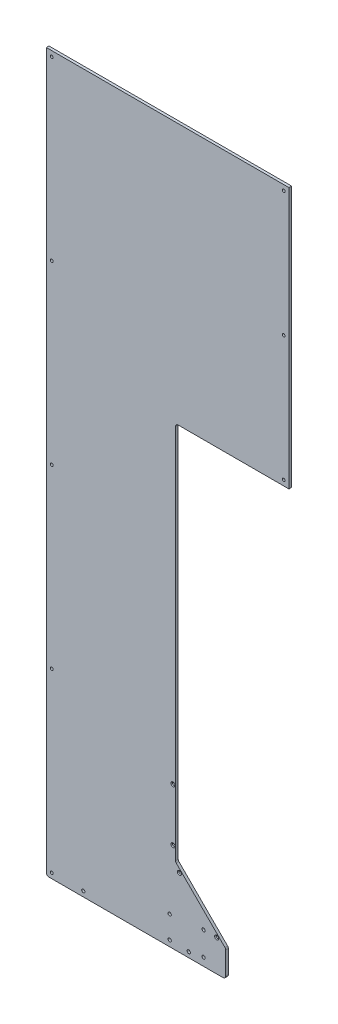
SolidWorks part; units mm, degrees
material "PC High Viscosity"
ref_plane "Front Plane" through (0, 0, 0) normal (0, 0, 1) x (1, 0, 0)
ref_plane "Top Plane" through (0, 0, 0) normal (0, 1, 0) x (1, 0, 0)
ref_plane "Right Plane" through (0, 0, 0) normal (1, 0, 0) x (0, 0, -1)
sketch "Sketch2" plane through (0, 0, 0) normal (0, 0, 1) x (1, 0, 0)
  line L1 (0, 0) -> (584.2, 0)
  line L2 (0, 0) -> (0, 1727.2)
  line L3 (0, 1727.2) -> (584.2, 1727.2)
  line L4 (584.2, 0) -> (584.2, 1727.2)
  dimension "D1" = 584.2
  dimension "D2" = 1727.2
extrude "Boss-Extrude1" add sketch "Sketch2" along normal blind 6.35
sketch "Sketch3" plane through (0, 0, 6.35) normal (0, 0, 1) x (1, 0, 0)
  line L0 (584.2, 1098.55) -> (311.15, 1098.55)
  line L1 (584.2, 0) -> (584.2, 1727.2) construction
  line L2 (311.15, 1098.55) -> (311.15, 184.15)
  line L5 (431.8, 56.7648) -> (333.3633, 155.2015) construction
  line L6 (584.2, 0) -> (431.8, 0)
  line L7 (584.2, 0) -> (584.2, 1098.55)
  line L8 (584.2, 1727.2) -> (0, 1727.2) construction
  line L9 (0, 1727.2) -> (0, 0) construction
  line L10 (311.15, 184.15) -> (431.8, 63.5)
  line L11 (431.8, 63.5) -> (431.8, 0)
  circle A0 centre (584.2, 241.3) radius 241.3 construction
  dimension "D3" = 241.3
  dimension "D5" = 482.6
  dimension "D7" = 431.8
  dimension "D1" = 628.65
  dimension "D2" = 311.15
  dimension "D4" = 584.2
  dimension "D6" = 273.05
  dimension "D8" = 63.5
  dimension "D9" = 135
  dimension "D10" = 9.525
  dimension "D11" = 56.7648
  dimension "D12" = 170.6249
extrude "Cut-Extrude1" cut sketch "Sketch3" against normal through all
sketch "Sketch4" plane through (0, 0, 6.35) normal (0, 0, 1) x (1, 0, 0)
  line L0 (0, 1727.2) -> (0, 0) construction
  line L1 (584.2, 1098.55) -> (584.2, 1727.2) construction
  line L2 (584.2, 1727.2) -> (0, 1727.2) construction
  point P0 (12.7, 1714.5)
  point P1 (12.7, 1289.05)
  point P2 (12.7, 863.6)
  point P3 (12.7, 438.15)
  point P4 (12.7, 12.7)
  point P5 (571.5, 1111.25)
  point P6 (571.5, 1412.875)
  point P7 (571.5, 1714.5)
  dimension "D1" = 12.7
  dimension "D2" = 12.7
  dimension "D3" = 12.7
  dimension "D4" = 301.625
  dimension "D5" = 603.25
  dimension "D6" = 425.45
  dimension "D7" = 425.45
  dimension "D8" = 425.45
  dimension "D9" = 425.45
hole_wizard "H (0.266) Diameter Hole1" positions "Sketch5" profile "Sketch6" hole size "H" standard "ANSI Inch" end condition through all
sketch "Sketch5" plane through (0, 0, 6.35) normal (0, 0, 1) x (1, 0, 0)
  point P0 (12.7, 1714.5)
  point P3 (12.7, 1289.05)
  point P6 (12.7, 863.6)
  point P9 (12.7, 438.15)
  point P12 (12.7, 12.7)
  point P15 (571.5, 1111.25)
  point P18 (571.5, 1412.875)
  point P21 (571.5, 1714.5)
sketch "Sketch6" plane through (12.7, 1714.5, 6.35) normal (1, 0, 0) x (0, -1, 0)
  line L0 (0, 0) -> (0, 6.35)
  line L1 (0, 6.35) -> (3.3782, 6.35)
  line L2 (3.3782, 6.35) -> (3.3782, 0)
  line L5 (3.3782, 0) -> (0, 0)
  line L11 (0, -6.35) -> (0, 107.95) construction
  dimension "Thru Hole Dia." = 6.7564
  dimension "Thru Hole Depth" = 6.35
fillet "Fillet1" radius 6.35 5 edges at (311.15, 1098.55, 3.175) (431.8, 63.5, 3.175) (311.15, 184.15, 3.175) (0, 0, 3.175) (431.8, 0, 3.175)
sketch "Sketch7" plane through (0, 0, 6.35) normal (0, 0, 1) x (1, 0, 0)
  line L0 (6.35, 0) -> (425.45, 0) construction
  line L1 (0, 1727.2) -> (0, 6.35) construction
  circle A0 centre (88.9, 12.7) radius 3.9688
  circle A1 centre (342.9, 12.7) radius 3.9688
  dimension "D1" = 12.7
  dimension "D3" = 7.9375
  dimension "D2" = 254
  dimension "D4" = 88.9
extrude "Cut-Extrude2" cut sketch "Sketch7" against normal blind 12.7
sketch "Sketch8" plane through (0, 0, 6.35) normal (0, 0, 1) x (1, 0, 0)
  line L0 (311.15, 1092.2) -> (311.15, 186.7803) construction
  line L1 (6.35, 0) -> (425.45, 0) construction
  circle A0 centre (304.8, 342.9) radius 3.3655 construction
  circle A1 centre (304.8, 215.9) radius 3.3655 construction
  point P5 (304.8, 342.9)
  point P8 (304.8, 215.9)
  dimension "D1" = 6.35
  dimension "D2" = 6.731
  dimension "D3" = 127
  dimension "D4" = 215.9
sketch "Sketch10" plane through (0, 0, 6.35) normal (0, 0, 1) x (1, 0, 0)
  line L0 (320.3172, 166.0026) -> (410.1197, 76.2) construction
  line L2 (313.0099, 182.2901) -> (429.9401, 65.3599) construction
  line L3 (6.35, 0) -> (425.45, 0) construction
  circle A0 centre (320.3172, 166.0026) radius 3.3655 construction
  circle A1 centre (410.1197, 76.2) radius 3.3655 construction
  point P9 (410.1197, 76.2)
  point P10 (320.3172, 166.0026)
  dimension "D1" = 127
  dimension "D4" = 6.731
  dimension "D2" = 76.2
  dimension "D3" = 6.35
hole_wizard "CSK for #10 Flat Head Machine Screw (100)1" positions "Sketch11" profile "Sketch12" countersink size "#10" standard "ANSI Inch" end condition up to next
sketch "Sketch11" plane through (0, 0, 6.35) normal (0, 0, 1) x (1, 0, 0)
  point P0 (304.8, 342.9)
  point P3 (304.8, 215.9)
  point P6 (320.3172, 166.0026)
  point P9 (410.1197, 76.2)
sketch "Sketch12" plane through (304.8, 342.9, 6.35) normal (1, 0, 0) x (0, -1, 0)
  line L0 (0, 0) -> (0, 6.35)
  line L1 (0, 6.35) -> (2.8067, 6.35)
  line L2 (2.8067, 6.35) -> (2.8067, 1.7477)
  line L3 (2.8067, 1.7477) -> (4.8895, 0)
  line L5 (4.8895, 0) -> (0, 0)
  line L6 (-2.8067, 1.7477) -> (-4.8895, 0) construction
  line L11 (0, -6.35) -> (0, 107.95) construction
  dimension "Thru Hole Dia." = 5.6134
  dimension "Thru Hole Depth" = 6.35
  dimension "Near C'Sink Dia." = 9.779
  dimension "Near C'Sink Angle" = 100
sketch "Sketch13" plane through (0, 0, 0) normal (0, 0, -1) x (-1, 0, 0)
  line L0 (-431.8, 6.35) -> (-431.8, 76.2) construction
  line L1 (-6.35, 0) -> (-425.45, 0) construction
  line L2 (-25.4, 0) -> (-425.45, 0) construction
  circle A0 centre (-378.4676, 76.2) radius 3.937
  circle A1 centre (-378.4676, 19.05) radius 3.937
  dimension "D1" = 7.874
  dimension "D2" = 7.874
  dimension "D3" = 76.2
  dimension "D4" = 19.05
  dimension "D5" = 53.3324
extrude "Cut-Extrude3" cut sketch "Sketch13" against normal through all
hole_wizard "5/16 (0.3125) Diameter Hole1" positions "Sketch14" profile "Sketch15" hole size "5/16" standard "ANSI Inch" end condition through all
sketch "Sketch14" plane through (0, 0, 6.35) normal (0, 0, 1) x (1, 0, 0)
  line L0 (6.35, 0) -> (425.45, 0) construction
  line L1 (0, 1727.2) -> (0, 6.35) construction
  point P0 (296.8625, 14.2875)
  point P2 (296.8625, 68.2625)
  point P9 (0, 0)
  dimension "D1" = 14.2875
  dimension "D2" = 296.8625
  dimension "D3" = 53.975
sketch "Sketch15" plane through (296.8625, 14.2875, 6.35) normal (1, 0, 0) x (0, -1, 0)
  line L0 (0, 0) -> (0, 6.35)
  line L1 (0, 6.35) -> (3.9687, 6.35)
  line L2 (3.9687, 6.35) -> (3.9687, 0)
  line L5 (3.9687, 0) -> (0, 0)
  line L11 (0, -6.35) -> (0, 107.95) construction
  dimension "Thru Hole Dia." = 7.9375
  dimension "Thru Hole Depth" = 6.35
